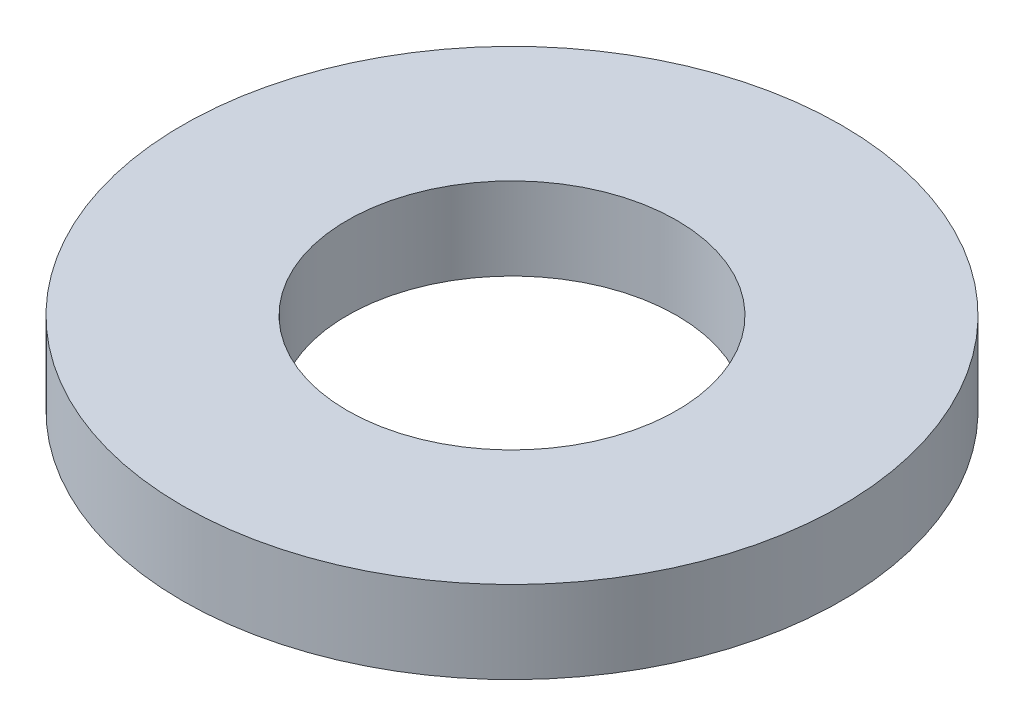
SolidWorks part; units mm, degrees
ref_plane "Front Plane" through (0, 0, 0) normal (0, 0, 1) x (1, 0, 0)
ref_plane "Top Plane" through (0, 0, 0) normal (0, 1, 0) x (1, 0, 0)
ref_plane "Right Plane" through (0, 0, 0) normal (1, 0, 0) x (0, 0, -1)
sketch "Sketch1" plane through (0, 0, 0) normal (0, 1, 0) x (1, 0, 0)
  circle A0 centre (0, 0) radius 12.7
  circle A1 centre (0, 0) radius 25.4
  dimension "D1" = 50.8
  dimension "D2" = 25.4
extrude "Boss-Extrude1" add sketch "Sketch1" along normal blind 6.35
